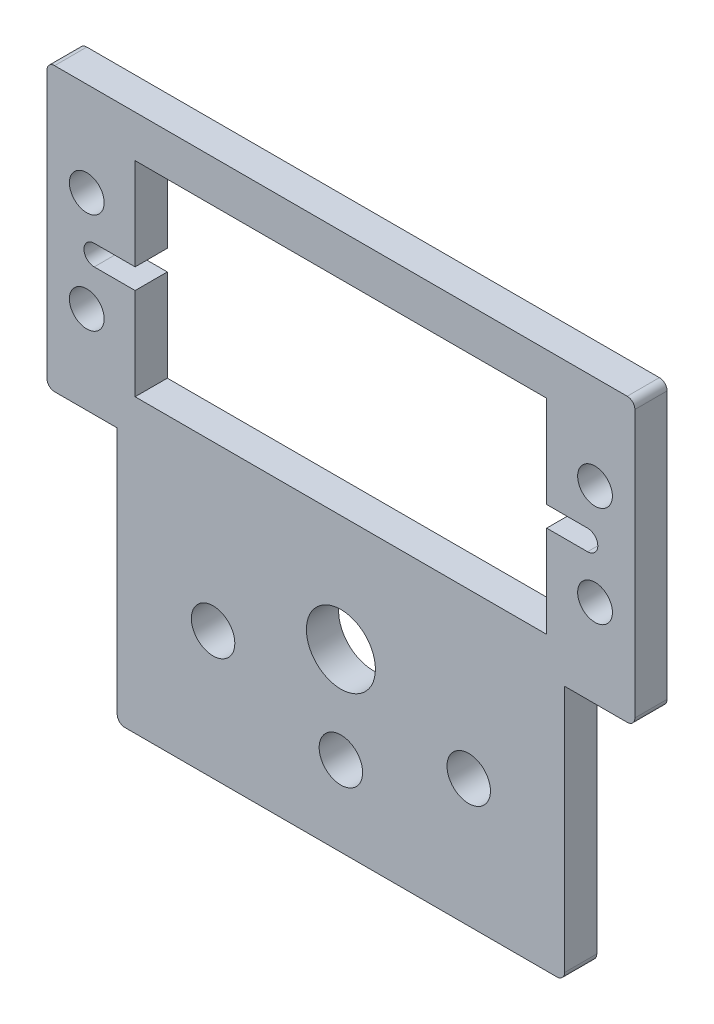
SolidWorks part; units mm, degrees
ref_plane "Front Plane" through (0, 0, 0) normal (0, 0, 1) x (1, 0, 0)
ref_plane "Top Plane" through (0, 0, 0) normal (0, 1, 0) x (1, 0, 0)
ref_plane "Right Plane" through (0, 0, 0) normal (1, 0, 0) x (0, 0, -1)
sketch "Sketch1" plane through (0, 0, 0) normal (0, 0, 1) x (1, 0, 0)
  line L0 (22.225, 12.7) -> (22.225, 0) construction
  line L3 (0, 0) -> (44.45, 0)
  line L5 (9.525, 12.7) -> (34.925, 12.7) construction
  line L6 (1.778, 49.2911) -> (42.672, 49.2911)
  line L7 (1.778, 49.2911) -> (1.778, 28.9711)
  line L8 (1.778, 28.9711) -> (42.672, 28.9711)
  line L9 (42.672, 49.2911) -> (42.672, 28.9711)
  line L10 (47.475, 44.1311) -> (47.475, 34.1311) construction
  line L11 (-3.025, 44.1311) -> (-3.025, 34.1311) construction
  line L12 (47.475, 39.1311) -> (-3.025, 39.1311) construction
  line L13 (0, 25.4) -> (44.45, 25.4) construction
  line L14 (0, 0) -> (0, 25.4)
  line L15 (0, 25.4) -> (-6.985, 25.4)
  line L16 (-6.985, 25.4) -> (-6.985, 53.4647)
  line L17 (44.45, 0) -> (44.45, 25.4)
  line L18 (44.45, 25.4) -> (51.435, 25.4)
  line L20 (-6.985, 53.4647) -> (51.435, 53.4647)
  line L21 (51.435, 53.4647) -> (51.435, 25.4)
  line L22 (22.225, 17.4625) -> (22.225, 25.4) construction
  line L23 (22.225, 53.4647) -> (22.225, 49.2911) construction
  line L24 (22.225, 49.2911) -> (22.225, 28.9711) construction
  line L25 (-6.985, 39.1311) -> (-3.025, 39.1311) construction
  line L26 (47.475, 39.1311) -> (51.435, 39.1311) construction
  circle A0 centre (9.525, 12.7) radius 2.159
  circle A1 centre (34.925, 12.7) radius 2.159
  circle A2 centre (47.475, 34.1311) radius 1.7272
  circle A3 centre (-3.025, 44.1311) radius 1.7272
  circle A4 centre (-3.025, 34.1311) radius 1.7272
  circle A5 centre (47.475, 44.1311) radius 1.7272
  circle A6 centre (22.225, 17.4625) radius 3.429
  circle A7 centre (32.075, 39.1311) radius 3.429 construction
  circle A8 centre (22.225, 7.9375) radius 2.159
  point P13 (42.672, 39.1311)
  point P25 (22.225, 39.1311)
  dimension "D5" = 4.318
  dimension "D10" = 3.4544
  dimension "D13" = 6.858
  dimension "D11" = 17.4625
  dimension "D14" = 23.8023
  dimension "D16" = 9.525
  dimension "D1" = 44.45
  dimension "D2" = 25.4
  dimension "D3" = 25.4
  dimension "D4" = 12.7
  dimension "D6" = 20.32
  dimension "D7" = 40.894
  dimension "D8" = 10
  dimension "D9" = 50.5
  dimension "D12" = 58.42
  dimension "D15" = 15.4
  dimension "D17" = 4.1735
extrude "Boss-Extrude1" add sketch "Sketch1" along normal blind 3.2004
sketch "Sketch2" plane through (0, 0, 3.2004) normal (0, 0, 1) x (1, 0, 0)
  line L2 (1.778, 49.2911) -> (1.778, 28.9711) construction
  line L3 (42.672, 28.9711) -> (42.672, 49.2911) construction
  line L4 (-2.286, 40.1471) -> (1.778, 40.1471)
  line L5 (-2.286, 40.1471) -> (-2.286, 38.1151) construction
  line L7 (-2.286, 38.1151) -> (1.778, 38.1151)
  line L8 (1.778, 40.1471) -> (1.778, 38.1151)
  line L9 (42.672, 40.1471) -> (46.736, 40.1471)
  line L10 (42.672, 40.1471) -> (42.672, 38.1151)
  line L11 (42.672, 38.1151) -> (46.736, 38.1151)
  line L12 (46.736, 40.1471) -> (46.736, 38.1151) construction
  arc A6 (46.736, 40.1471) -> (46.736, 38.1151) centre (46.736, 39.1311) cw
  arc A7 (-2.286, 40.1471) -> (-2.286, 38.1151) centre (-2.286, 39.1311) ccw
  point P22 (1.778, 39.1311)
  point P23 (42.672, 39.1311)
  dimension "D4" = 4.064
  dimension "D5" = 2.032
extrude "Cut-Extrude1" cut sketch "Sketch2" against normal up to surface (3.2004 mm away) up to face at (25.654, 17.4625, 0)
fillet "Fillet1" radius 0.762 6 edges at (44.45, 0, 1.6002) (51.435, 25.4, 1.6002) (51.435, 53.4647, 1.6002) (0, 0, 1.6002) (-6.985, 25.4, 1.6002) (-6.985, 53.4647, 1.6002)
